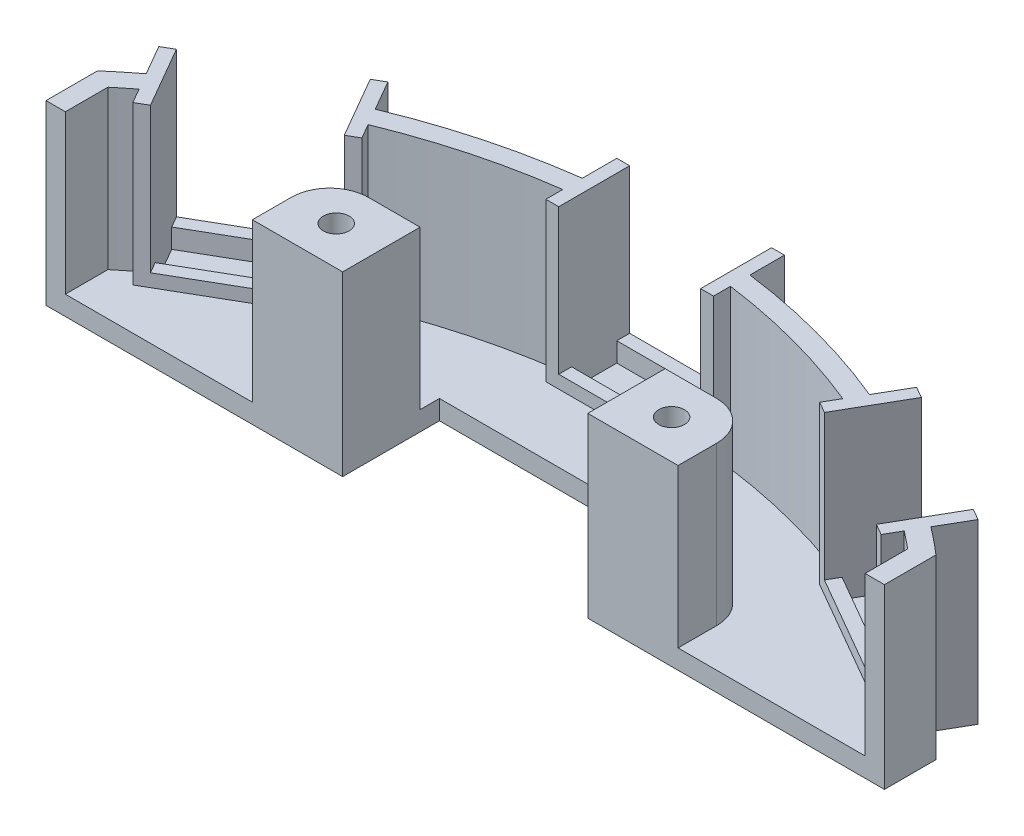
SolidWorks part; units mm, degrees
ref_plane "前视基准面" through (0, 0, 0) normal (0, 0, 1) x (1, 0, 0)
ref_plane "上视基准面" through (0, 0, 0) normal (0, 1, 0) x (1, 0, 0)
ref_plane "右视基准面" through (0, 0, 0) normal (1, 0, 0) x (0, 0, -1)
sketch "草图1" plane through (0, 0, 0) normal (0, 1, 0) x (1, 0, 0)
  line L0 (-100, 0) -> (100, 0)
  line L1 (0, 0) -> (0, 99)
  line L2 (19, 17) -> (-19, 17)
  line L3 (19, 17) -> (19, 83)
  line L4 (19, 83) -> (-19, 83)
  line L5 (-19, 17) -> (-19, 83)
  line L6 (19, 17) -> (-19, 83) construction
  line L7 (19, 83) -> (-19, 17) construction
  line L8 (0, 0) -> (49.5, 85.7365)
  line L9 (0, 0) -> (-49.5, 85.7365)
  line L10 (-150.1814, 68) -> (135.9874, 68)
  line L12 (-63.5083, 83.9997) -> (-40.9917, 96.9997)
  line L13 (-63.5083, 83.9997) -> (-58.0083, 74.4734)
  line L14 (-58.0083, 74.4734) -> (-35.4917, 87.4734)
  line L15 (-40.9917, 96.9997) -> (-35.4917, 87.4734)
  line L16 (-63.5083, 83.9997) -> (-35.4917, 87.4734) construction
  line L17 (-13, 104.5) -> (13, 104.5)
  line L18 (-13, 104.5) -> (-13, 93.5)
  line L19 (-13, 93.5) -> (13, 93.5)
  line L20 (13, 104.5) -> (13, 93.5)
  line L21 (-13, 104.5) -> (13, 93.5) construction
  line L22 (-13, 93.5) -> (13, 104.5) construction
  line L23 (40.9917, 96.9997) -> (63.5083, 83.9997)
  line L24 (40.9917, 96.9997) -> (35.4917, 87.4734)
  line L25 (35.4917, 87.4734) -> (58.0083, 74.4734)
  line L26 (63.5083, 83.9997) -> (58.0083, 74.4734)
  line L27 (40.9917, 96.9997) -> (58.0083, 74.4734) construction
  line L28 (35.4917, 87.4734) -> (63.5083, 83.9997) construction
  line L29 (-65, 114.503) -> (-65, -14.8084)
  line L30 (65, 110.1512) -> (65, -26.6205)
  line L31 (-58.0083, 74.4734) -> (-40.9917, 96.9997) construction
  circle A0 centre (0, 0) radius 100
  point P5 (0, 50)
  dimension "D1" = 200
  dimension "D2" = 50
  dimension "D3" = 66
  dimension "D4" = 38
  dimension "D5" = 99
  dimension "D6" = 99
  dimension "D7" = 99
  dimension "D8" = 30
  dimension "D9" = 30
  dimension "D10" = 26
  dimension "D11" = 11
  dimension "D12" = 26
  dimension "D13" = 11
  dimension "D14" = 26
  dimension "D15" = 11
  dimension "D16" = 68
  dimension "D17" = 65
  dimension "D18" = 65
extrude "底座" add sketch "草图1" against normal blind 3 contours L13 A0 L29 L10 L9 L14 | L18 A0 L15 L14 L9 L10 L5 L4 L1 L19 | L24 A0 L20 L19 L1 L4 L3 L10 L8 L25 | L30 A0 L26 L25 L8 L10
sketch "草图5" plane through (0, 0, 0) normal (0, 1, 0) x (1, 0, 0)
  line L0 (-13, 104.5) -> (-11, 104.5)
  line L2 (-13, 104.5) -> (-13, 93.5)
  line L4 (-11, 104.5) -> (-11, 93.5)
  line L6 (-13, 93.5) -> (-11, 93.5)
  line L7 (-13, 104.5) -> (13, 104.5) construction
  line L9 (13, 104.5) -> (11, 104.5)
  line L16 (13, 104.5) -> (13, 93.5)
  line L17 (11, 104.5) -> (11, 93.5)
  line L18 (13, 93.5) -> (11, 93.5)
  line L19 (40.9917, 96.9997) -> (42.7237, 95.9997)
  line L20 (40.9917, 96.9997) -> (35.4917, 87.4734)
  line L21 (42.7237, 95.9997) -> (37.2237, 86.4734)
  line L22 (35.4917, 87.4734) -> (37.2237, 86.4734)
  line L23 (40.9917, 96.9997) -> (63.5083, 83.9997) construction
  line L24 (63.5083, 83.9997) -> (61.7763, 84.9997)
  line L25 (63.5083, 83.9997) -> (58.0083, 74.4734)
  line L26 (61.7763, 84.9997) -> (56.2763, 75.4734)
  line L27 (58.0083, 74.4734) -> (56.2763, 75.4734)
  line L28 (-40.9917, 96.9997) -> (-42.7237, 95.9997)
  line L29 (-40.9917, 96.9997) -> (-35.4917, 87.4734)
  line L30 (-42.7237, 95.9997) -> (-37.2237, 86.4734)
  line L31 (-35.4917, 87.4734) -> (-37.2237, 86.4734)
  line L32 (-63.5083, 83.9997) -> (-40.9917, 96.9997) construction
  line L33 (-62, 27.521) -> (-62, 157.7235)
  line L34 (62, 18.3586) -> (62, 161.5814)
  line L35 (65, 75.9934) -> (65, 68) construction
  line L36 (-65, 75.9934) -> (-65, 68) construction
  line L37 (-63.5083, 83.9997) -> (-61.7763, 84.9997)
  line L38 (-19, 68) -> (-33, 68)
  line L39 (-19, 68) -> (-19, 80)
  line L40 (-19, 80) -> (-33, 80)
  line L41 (-33, 68) -> (-33, 80)
  line L42 (19, 68) -> (33, 68)
  line L43 (19, 68) -> (19, 80)
  line L44 (19, 80) -> (33, 80)
  line L45 (33, 68) -> (33, 80)
  line L46 (-63.5083, 83.9997) -> (-58.0083, 74.4734)
  line L47 (-61.7763, 84.9997) -> (-56.2763, 75.4734)
  line L48 (-58.0083, 74.4734) -> (-56.2763, 75.4734)
  circle A24 centre (0, 0) radius 97
  arc M10 (65, 75.9934) -> (60.834, 79.3676) centre (0, 0) ccw
  arc M14 (38.3174, 92.3676) -> (13, 99.1514) centre (0, 0) ccw
  arc M18 (-13, 99.1514) -> (-38.3174, 92.3676) centre (0, 0) ccw
  arc M22 (-60.834, 79.3676) -> (-65, 75.9934) centre (0, 0) ccw
  line M23 (-65, 75.9934) -> (-65, 68)
  line M24 (-65, 68) -> (-19, 68)
  line M25 (-19, 68) -> (-19, 83)
  line M27 (19, 83) -> (19, 68)
  line M28 (19, 68) -> (65, 68)
  line M29 (65, 68) -> (65, 75.9934)
  dimension "D14" = 194
  dimension "D2" = 2
  dimension "D3" = 2
  dimension "D4" = 11
  dimension "D5" = 11
  dimension "D6" = 2
  dimension "D7" = 2
  dimension "D8" = 2
  dimension "D9" = 2
  dimension "D10" = 11
  dimension "D11" = 11
  dimension "D12" = 3
  dimension "D13" = 3
  dimension "D15" = 14
  dimension "D16" = 12
  dimension "D17" = 12
  dimension "D18" = 14
  dimension "D19" = 11
  dimension "D20" = 11
extrude "侧壁" add sketch "草图5" along normal blind 24.5 contours L41 L40 M24 M25 | L45 L44 M28 M27 | L33 A24 M23 M24 | A24 L33 M22 M23 | A24 L46 L33 M22 | A24 L2 L29 M18 | A24 L20 L16 M14 | A24 L34 L25 M10 | A24 L34 M29 M10 | A24 L34 M29 M28
sketch "草图9" plane through (0, 0, 0) normal (0, 1, 0) x (1, 0, 0)
  line L0 (-56.2763, 75.4734) -> (-37.2237, 86.4734)
  line L1 (-11, 93.5) -> (11, 93.5)
  line L2 (37.2237, 86.4734) -> (56.2763, 75.4734)
  line M16 (56.2763, 75.4734) -> (61.7763, 84.9997)
  line M17 (61.7763, 84.9997) -> (42.7237, 95.9997)
  line M18 (42.7237, 95.9997) -> (37.2237, 86.4734)
  line M24 (11, 93.5) -> (11, 104.5)
  line M25 (11, 104.5) -> (-11, 104.5)
  line M26 (-11, 104.5) -> (-11, 93.5)
  line M32 (-37.2237, 86.4734) -> (-42.7237, 95.9997)
  line M33 (-42.7237, 95.9997) -> (-61.7763, 84.9997)
  line M34 (-61.7763, 84.9997) -> (-56.2763, 75.4734)
extrude "卡槽" add sketch "草图9" along normal blind 2 separate body contours L0 M34 M32 M33 | L1 M26 M24 M25 | L2 M18 M16 M17
sketch "草图11" plane through (0, 2, 0) normal (0, 1, 0) x (1, 0, 0)
  line L0 (0, 0) -> (0, 99)
  line L1 (0, 0) -> (49.5, 85.7365)
  line L2 (0, 0) -> (-49.5, 85.7365)
  line L4 (-60.7763, 83.2676) -> (-41.7237, 94.2676)
  line L5 (-60.7763, 83.2676) -> (-57.2763, 77.2054)
  line L6 (-57.2763, 77.2054) -> (-38.2237, 88.2054)
  line L7 (-41.7237, 94.2676) -> (-38.2237, 88.2054)
  line L8 (-60.7763, 83.2676) -> (-38.2237, 88.2054) construction
  line L9 (-57.2763, 77.2054) -> (-41.7237, 94.2676) construction
  line L10 (-11, 102.5) -> (11, 102.5)
  line L11 (-11, 102.5) -> (-11, 95.5)
  line L12 (-11, 95.5) -> (11, 95.5)
  line L13 (11, 102.5) -> (11, 95.5)
  line L14 (-11, 102.5) -> (11, 95.5) construction
  line L15 (-11, 95.5) -> (11, 102.5) construction
  line L16 (41.7237, 94.2676) -> (60.7763, 83.2676)
  line L17 (41.7237, 94.2676) -> (38.2237, 88.2054)
  line L18 (38.2237, 88.2054) -> (57.2763, 77.2054)
  line L19 (60.7763, 83.2676) -> (57.2763, 77.2054)
  line L20 (41.7237, 94.2676) -> (57.2763, 77.2054) construction
  line L21 (38.2237, 88.2054) -> (60.7763, 83.2676) construction
  dimension "D1" = 30
  dimension "D2" = 30
  dimension "D3" = 99
  dimension "D4" = 99
  dimension "D5" = 99
  dimension "D6" = 22
  dimension "D7" = 7
  dimension "D8" = 7
  dimension "D9" = 22
  dimension "D10" = 22
  dimension "D11" = 7
extrude "开口" cut sketch "草图11" against normal blind 3
sketch "草图6" plane through (0, -3, 0) normal (0, -1, 0) x (1, 0, 0)
  circle A0 centre (-26, -74) radius 2
  circle A1 centre (26, -74) radius 2
  dimension "D1" = 4
  dimension "D2" = 4
  dimension "D3" = 74
  dimension "D4" = 74
  dimension "D5" = 26
  dimension "D6" = 26
extrude "螺丝孔" cut sketch "草图6" against normal through all
fillet "圆角2" radius 6 2 edges at (-33, 12.25, -80) (33, 12.25, -80)
